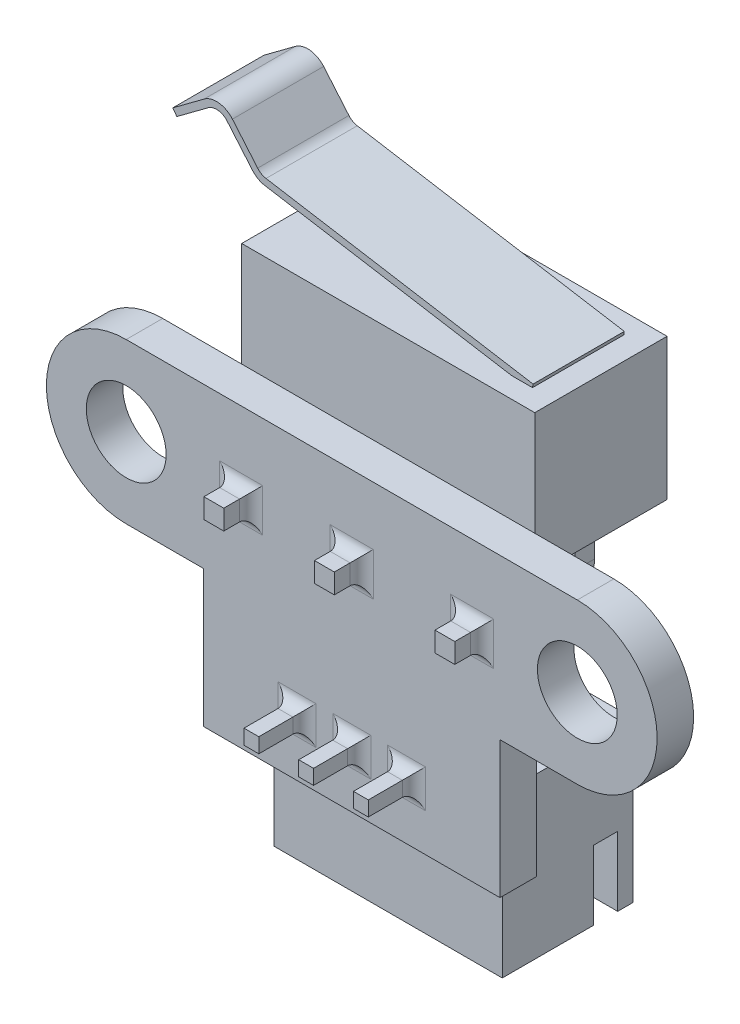
SolidWorks part; units mm, degrees
ref_plane "Front Plane" through (0, 0, 0) normal (0, 0, 1) x (1, 0, 0)
ref_plane "Top Plane" through (0, 0, 0) normal (0, 1, 0) x (1, 0, 0)
ref_plane "Right Plane" through (0, 0, 0) normal (1, 0, 0) x (0, 0, -1)
sketch "Sketch1" plane through (0, 0, 0) normal (0, 0, 1) x (1, 0, 0)
  line L0 (-9.89, 0) -> (9.89, 0) construction
  line L1 (-9.89, 3.5) -> (9.89, 3.5)
  line L2 (-9.89, -3.5) -> (-6.5, -3.5)
  line L3 (6.5, -3.5) -> (9.89, -3.5)
  line L5 (-6.5, -3.5) -> (-6.5, -9.5)
  line L6 (-6.5, -9.5) -> (6.5, -9.5)
  line L7 (6.5, -3.5) -> (6.5, -9.5)
  line L8 (0, 0) -> (0, -9.5) construction
  arc A0 (-9.89, 3.5) -> (-9.89, -3.5) centre (-9.89, 0) ccw
  arc A1 (9.89, -3.5) -> (9.89, 3.5) centre (9.89, 0) ccw
  circle A2 centre (-9.89, 0) radius 1.75
  circle A3 centre (9.89, 0) radius 1.75
  dimension "D2" = 26.78
  dimension "D5" = 3.5
  dimension "D1" = 7
  dimension "D3" = 13
  dimension "D4" = 13
extrude "Boss-Extrude1" add sketch "Sketch1" along normal blind 1.6
sketch "Sketch2" plane through (0, 0, 0) normal (0, 0, -1) x (-1, 0, 0)
  line L0 (0, 0) -> (0, 1.88) construction
  line L1 (-6.425, 1.88) -> (6.425, 1.88)
  line L2 (-6.425, 1.88) -> (-6.425, 8.08)
  line L3 (-6.425, 8.08) -> (6.425, 8.08)
  line L4 (6.425, 1.88) -> (6.425, 8.08)
  line L5 (-9.89, 3.5) -> (9.89, 3.5) construction
  dimension "D1" = 12.85
  dimension "D2" = 6.2
  dimension "D3" = 4.58
extrude "Boss-Extrude2" add sketch "Sketch2" along normal blind 5.8
ref_plane "Plane1" through (0, 0, -2.9) normal (0, 0, 1) x (1, 0, 0)
sketch "Sketch3" plane through (0, 0, -2.9) normal (0, 0, 1) x (1, 0, 0)
  line L0 (5.425, 8.08) -> (-6.2837, 10.034) construction
  line L1 (-6.425, 8.08) -> (6.425, 8.08) construction
  line L2 (-6.7398, 10.2931) -> (-7.8471, 11.6005) construction
  line L3 (-8.8832, 11.7195) -> (-10.2581, 10.6973) construction
  line L4 (6.425, 8.08) -> (6.425, 3.5) construction
  line L5 (5.4497, 8.228) -> (-6.2591, 10.182)
  line L6 (-6.6253, 10.3901) -> (-7.7326, 11.6975)
  line L7 (-8.9727, 11.8399) -> (-10.3476, 10.8177)
  line L8 (5.4003, 7.932) -> (-6.3084, 9.8861)
  line L9 (-6.8542, 10.1962) -> (-7.9615, 11.5036)
  line L10 (-8.7937, 11.5992) -> (-10.1686, 10.5769)
  line L11 (5.4497, 8.228) -> (5.4003, 7.932)
  line L12 (-10.3476, 10.8177) -> (-10.1686, 10.5769)
  arc A0 (-6.2837, 10.034) -> (-6.7398, 10.2931) centre (-6.1583, 10.7856) cw construction
  arc A1 (-7.8471, 11.6005) -> (-8.8832, 11.7195) centre (-8.4286, 11.108) ccw construction
  arc A2 (-6.2591, 10.182) -> (-6.6253, 10.3901) centre (-6.1583, 10.7856) cw
  arc A3 (-7.7326, 11.6975) -> (-8.9727, 11.8399) centre (-8.4286, 11.108) ccw
  arc A4 (-6.3084, 9.8861) -> (-6.8542, 10.1962) centre (-6.1583, 10.7856) cw
  arc A5 (-7.9615, 11.5036) -> (-8.7937, 11.5992) centre (-8.4286, 11.108) ccw
  point P13 (-6.5593, 10.08)
  point P16 (-8.3093, 12.1463)
  dimension "D6" = 0.762
  dimension "D1" = 1
  dimension "D2" = 15.9
  dimension "D3" = 3.75
  dimension "D4" = 1.75
  dimension "D5" = 2
  dimension "D7" = 0.15
  dimension "D8" = 0.15
extrude "Boss-Extrude3" add sketch "Sketch3" along normal mid plane 4
sketch "Sketch4" plane through (0, 1.88, 0) normal (0, -1, 0) x (1, 0, 0)
  line L0 (0, 0) -> (0, -2.9) construction
  line L1 (-5.2825, -2.465) -> (-4.4125, -2.465)
  line L2 (-5.2825, -2.465) -> (-5.2825, -3.335)
  line L3 (-5.2825, -3.335) -> (-4.4125, -3.335)
  line L4 (-4.4125, -2.465) -> (-4.4125, -3.335)
  line L5 (-0.435, -2.465) -> (0.435, -2.465)
  line L6 (-0.435, -2.465) -> (-0.435, -3.335)
  line L7 (-0.435, -3.335) -> (0.435, -3.335)
  line L8 (0.435, -2.465) -> (0.435, -3.335)
  line L9 (4.8475, -2.465) -> (5.7175, -2.465)
  line L10 (4.8475, -2.465) -> (4.8475, -3.335)
  line L11 (4.8475, -3.335) -> (5.7175, -3.335)
  line L12 (5.7175, -2.465) -> (5.7175, -3.335)
  line L13 (-0.435, -2.465) -> (0.435, -3.335) construction
  line L14 (0, -2.9) -> (-4.4125, -2.9) construction
  line L15 (0.435, -2.9) -> (4.8475, -2.9) construction
  line L16 (-6.425, -5.8) -> (-6.425, 0) construction
  point P22 (-6.425, -2.9)
  dimension "D1" = 0.87
  dimension "D2" = 11
sketch "Sketch5" plane through (0, 0, 0) normal (1, 0, 0) x (0, 0, -1)
  line L0 (2.9, 1.88) -> (2.9, 0.508)
  line L1 (2.465, 1.88) -> (3.335, 1.88) construction
  line L2 (2.392, 0) -> (-2.8, 0)
  line L5 (-1.6, 3.5) -> (-1.6, -3.5) construction
  arc A0 (2.9, 0.508) -> (2.392, 0) centre (2.392, 0.508) cw
  dimension "D1" = 0.508
  dimension "D2" = 1.2
sweep "Sweep3" add profiles "Sketch4" path "Sketch5"
sketch "Sketch6" plane through (0, 0, 0) normal (0, 0, -1) x (-1, 0, 0)
  line L0 (0, -7.1) -> (0, 0) construction
  line L1 (-5, -7.1) -> (5, -7.1)
  line L2 (-5, -7.1) -> (-5, -14.1)
  line L3 (-5, -14.1) -> (5, -14.1)
  line L4 (5, -7.1) -> (5, -14.1)
  line L5 (6.5, -9.5) -> (-6.5, -9.5) construction
  dimension "D1" = 10
  dimension "D2" = 7
  dimension "D3" = 4.6
extrude "Boss-Extrude4" add sketch "Sketch6" along normal blind 5.73
sketch "Sketch7" plane through (0, -14.1, 0) normal (0, -1, 0) x (1, 0, 0)
  line L8 (4.33, -0.67) -> (-4.33, -0.67)
  line L9 (-4.33, -0.67) -> (-4.33, -5.06)
  line L10 (-4.33, -5.06) -> (4.33, -5.06)
  line L11 (4.33, -5.06) -> (4.33, -0.67)
  line L12 (4.33, -0.67) -> (-4.33, -0.67)
  line L13 (-4.33, -0.67) -> (-4.33, -5.06)
  line L14 (-4.33, -5.06) -> (4.33, -5.06)
  line L15 (4.33, -5.06) -> (4.33, -0.67)
  dimension "D1" = 0.67
extrude "Cut-Extrude1" cut sketch "Sketch7" against normal blind 5.35
sketch "Sketch8" plane through (0, -14.1, 0) normal (0, -1, 0) x (-1, 0, 0)
  line L0 (4.33, 5.06) -> (-4.33, 5.06) construction
  line L1 (3.22, 5.06) -> (1.58, 5.06)
  line L2 (3.22, 5.06) -> (3.22, 5.73)
  line L3 (3.22, 5.73) -> (1.58, 5.73)
  line L4 (1.58, 5.06) -> (1.58, 5.73)
  line L5 (-5, 5.73) -> (5, 5.73) construction
  line L6 (1.58, 5.395) -> (-1.58, 5.395) construction
  line L7 (-1.58, 5.06) -> (-3.22, 5.06)
  line L8 (-1.58, 5.06) -> (-1.58, 5.73)
  line L9 (-1.58, 5.73) -> (-3.22, 5.73)
  line L10 (-3.22, 5.06) -> (-3.22, 5.73)
  line L11 (0, 5.395) -> (0, 0) construction
  point P18 (2.4, 5.06)
  dimension "D1" = 2.4
  dimension "D2" = 1.64
extrude "Cut-Extrude2" cut sketch "Sketch8" against normal blind 3.86
sketch "Sketch9" plane through (0, -14.1, 0) normal (0, -1, 0) x (1, 0, 0)
  line L0 (-5, -5.73) -> (-5, 0) construction
  line L1 (-4.33, -5.06) -> (-5, -5.06)
  line L2 (-4.33, -5.06) -> (-4.33, -3.99)
  line L3 (-4.33, -3.99) -> (-5, -3.99)
  line L4 (-5, -5.06) -> (-5, -3.99)
  line L5 (5, -5.73) -> (5, 0) construction
  line L6 (4.33, -5.06) -> (5, -5.06)
  line L7 (4.33, -5.06) -> (4.33, -3.99)
  line L8 (4.33, -3.99) -> (5, -3.99)
  line L9 (5, -5.06) -> (5, -3.99)
  dimension "D1" = 1.07
extrude "Cut-Extrude3" cut sketch "Sketch9" against normal blind 3.04
sketch "Sketch10" plane through (0, 0, 0) normal (1, 0, 0) x (0, 0, -1)
  line L0 (3.43, -13.43) -> (3.43, -7.508)
  line L2 (2.922, -7) -> (-3.6, -7)
  line L3 (-1.6, -9.5) -> (-1.6, -3.5) construction
  line L4 (5.73, -7.1) -> (5.73, -14.1) construction
  line L5 (-1.6, -9.5) -> (0, -9.5) construction
  line L6 (3.99, -14.1) -> (0, -14.1) construction
  arc A0 (3.43, -7.508) -> (2.922, -7) centre (2.922, -7.508) ccw
  dimension "D5" = 0.508
  dimension "D1" = 2
  dimension "D2" = 2.3
  dimension "D3" = 2.5
  dimension "D4" = 0.67
ref_plane "Plane2" through (0, -13.43, 0) normal (0, 1, 0) x (1, 0, 0)
sketch "Sketch11" plane through (0, -13.43, 0) normal (0, 1, 0) x (1, 0, 0)
  line L0 (0, 2.922) -> (0, -3.6) construction
  line L1 (-2.725, 3.755) -> (-2.075, 3.755)
  line L2 (-2.725, 3.755) -> (-2.725, 3.105)
  line L3 (-2.725, 3.105) -> (-2.075, 3.105)
  line L4 (-2.075, 3.755) -> (-2.075, 3.105)
  line L5 (-2.725, 3.755) -> (-2.075, 3.105) construction
  line L6 (-2.725, 3.105) -> (-2.075, 3.755) construction
  line L7 (-0.325, 3.755) -> (0.325, 3.755)
  line L8 (-0.325, 3.755) -> (-0.325, 3.105)
  line L9 (-0.325, 3.105) -> (0.325, 3.105)
  line L10 (0.325, 3.755) -> (0.325, 3.105)
  line L11 (-0.325, 3.755) -> (0.325, 3.105) construction
  line L12 (-0.325, 3.105) -> (0.325, 3.755) construction
  line L13 (-2.4, 5.06) -> (-2.4, 3.43) construction
  line L14 (2.075, 3.755) -> (2.725, 3.755)
  line L15 (2.075, 3.755) -> (2.075, 3.105)
  line L16 (2.075, 3.105) -> (2.725, 3.105)
  line L17 (2.725, 3.755) -> (2.725, 3.105)
  line L18 (2.075, 3.755) -> (2.725, 3.105) construction
  line L19 (2.075, 3.105) -> (2.725, 3.755) construction
  line L20 (-1.58, 5.06) -> (-3.22, 5.06) construction
  line L21 (-2.4, 3.43) -> (2.4, 3.43) construction
  point P0 (-2.4, 3.43)
  point P5 (0, 3.43)
  point P12 (2.4, 3.43)
  dimension "D1" = 0.65
sweep "Sweep4" add profiles "Sketch11" path "Sketch10"
fillet "Fillet1" radius 0.508 24 edges at (5.2825, -0.435, 1.6) (5.7175, 0, 1.6) (5.2825, 0.435, 1.6) (4.8475, 0, 1.6) (-0.435, 0, 1.6) (0, 0.435, 1.6) (0.435, 0, 1.6) (0, -0.435, 1.6) (-4.8475, -0.435, 1.6) (-4.4125, 0, 1.6) (-4.8475, 0.435, 1.6) (-5.2825, 0, 1.6) (-2.4, -7.325, 1.6) (-2.075, -7, 1.6) (-2.725, -7, 1.6) (-2.4, -6.675, 1.6) (-0.325, -7, 1.6) (0, -6.675, 1.6) (0.325, -7, 1.6) (0, -7.325, 1.6) (2.4, -7.325, 1.6) (2.075, -7, 1.6) (2.4, -6.675, 1.6) (2.725, -7, 1.6)
